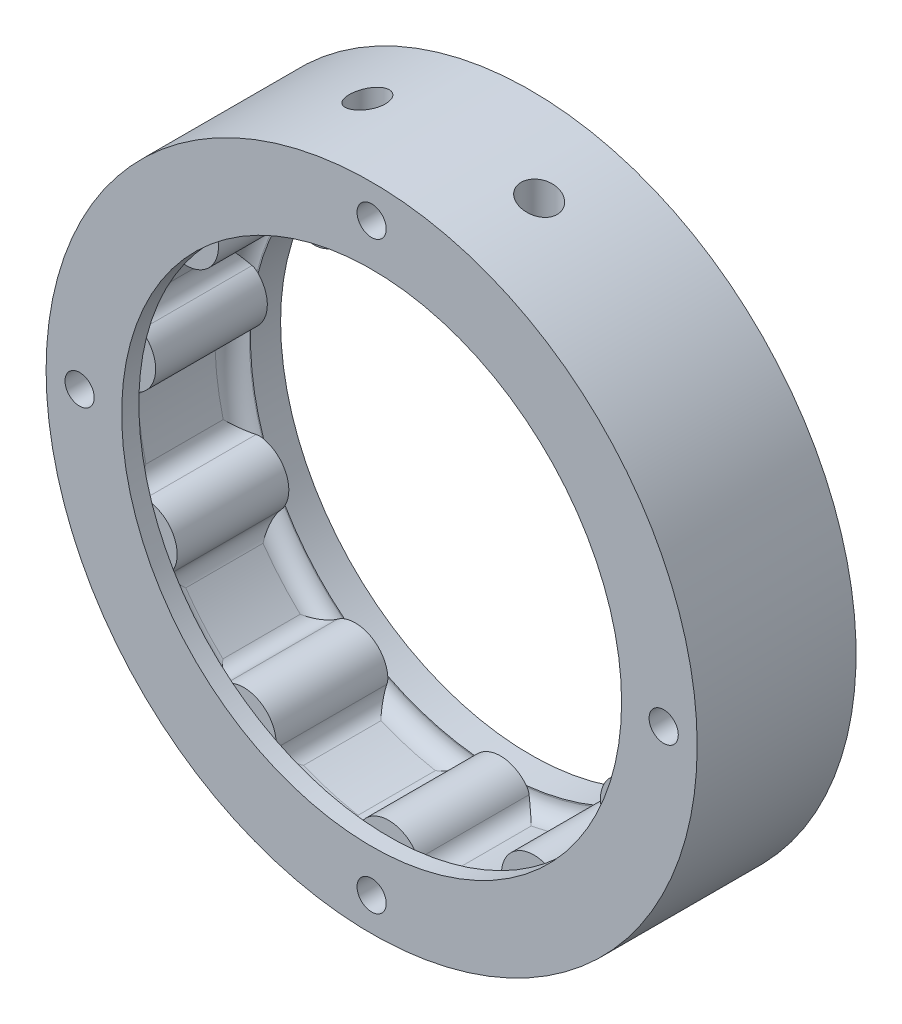
SolidWorks part; units mm, degrees
ref_plane "前视基准面" through (0, 0, 0) normal (0, 0, 1) x (1, 0, 0)
ref_plane "上视基准面" through (0, 0, 0) normal (0, 1, 0) x (1, 0, 0)
ref_plane "右视基准面" through (0, 0, 0) normal (1, 0, 0) x (0, 0, -1)
sketch "草图1" plane through (0, 0, 0) normal (0, 0, 1) x (1, 0, 0)
  arc A0 (-31.2338, 0.6797) -> (-29.7771, -9.4517) centre (0, 0) ccw
  arc A1 (3.7723, -31.0126) -> (-3.7723, -31.0126) centre (0, -31.2412) ccw
  arc A2 (-13.5933, -28.1289) -> (-19.9401, -24.05) centre (-16.8903, -26.2818) ccw
  arc A3 (-26.643, -16.3145) -> (-29.7771, -9.4517) centre (-28.418, -12.9781) ccw
  arc A4 (-31.2338, 0.6797) -> (-30.1601, 8.1474) centre (-30.9232, 4.4461) ccw
  arc A5 (-25.9081, 17.4581) -> (-20.9675, 23.1598) centre (-23.6105, 20.4586) ccw
  arc A6 (-12.3567, 28.6936) -> (-5.1178, 30.8191) centre (-8.8017, 29.9757) ccw
  arc A7 (5.1178, 30.8191) -> (12.3567, 28.6936) centre (8.8017, 29.9757) ccw
  arc A8 (20.9675, 23.1598) -> (25.9081, 17.4581) centre (23.6105, 20.4586) ccw
  arc A9 (30.1601, 8.1474) -> (31.2338, 0.6797) centre (30.9232, 4.4461) ccw
  arc A10 (29.7771, -9.4517) -> (26.643, -16.3145) centre (28.418, -12.9781) ccw
  arc A11 (19.9401, -24.05) -> (13.5933, -28.1289) centre (16.8903, -26.2818) ccw
  arc A13 (-25.9081, 17.4581) -> (-30.1601, 8.1474) centre (0, 0) ccw
  arc A14 (-12.3567, 28.6936) -> (-20.9675, 23.1598) centre (0, 0) ccw
  arc A15 (5.1178, 30.8191) -> (-5.1178, 30.8191) centre (0, 0) ccw
  arc A16 (20.9675, 23.1598) -> (12.3567, 28.6936) centre (0, 0) ccw
  arc A17 (30.1601, 8.1474) -> (25.9081, 17.4581) centre (0, 0) ccw
  arc A18 (29.7771, -9.4517) -> (31.2338, 0.6797) centre (0, 0) ccw
  arc A19 (-26.643, -16.3145) -> (-19.9401, -24.05) centre (0, 0) ccw
  arc A20 (-13.5933, -28.1289) -> (-3.7723, -31.0126) centre (0, 0) ccw
  arc A21 (3.7723, -31.0126) -> (13.5933, -28.1289) centre (0, 0) ccw
  arc A22 (19.9401, -24.05) -> (26.643, -16.3145) centre (0, 0) ccw
  circle A23 centre (0, -34) radius 1.7
  circle A24 centre (-34, 0) radius 1.7
  circle A25 centre (0, 34) radius 1.7
  circle A26 centre (34, 0) radius 1.7
  circle A29 centre (0, 0) radius 37.9
  point P28 (0, 0)
  point P52 (0, 0)
  dimension "D1" = 11
  dimension "D2" = 34
  dimension "D3" = 4
extrude "凸台-拉伸1" add sketch "草图1" along normal blind 13
sketch "草图2" plane through (0, 0, 0) normal (0, 0, -1) x (-1, 0, 0)
  circle A0 centre (0, 0) radius 29.1
  circle A1 centre (0, 0) radius 37.9
extrude "凸台-拉伸2" add sketch "草图2" along normal blind 3.5
sketch "草图3" plane through (0, 0, 13) normal (0, 0, 1) x (1, 0, 0)
  circle A0 centre (0, 0) radius 29.1
  circle A1 centre (0, 0) radius 37.9
extrude "凸台-拉伸3" add sketch "草图3" along normal blind 2
fillet "圆角1" radius 2 44 edges at (31.2338, 0.6797, 6.5) (30.9232, -4.4461, 13) (29.7771, -9.4517, 6.5) (30.9232, -4.4461, 0) (26.643, -16.3145, 6.5) (23.6105, -20.4586, 13) (19.9401, -24.05, 6.5) (23.6105, -20.4586, 0) (13.5933, -28.1289, 6.5) (8.8017, -29.9757, 13) (3.7723, -31.0126, 6.5) (8.8017, -29.9757, 0) (-3.7723, -31.0126, 6.5) (-8.8017, -29.9757, 13) (-13.5933, -28.1289, 6.5) (-8.8017, -29.9757, 0) (-19.9401, -24.05, 6.5) (-23.6105, -20.4586, 13) (-26.643, -16.3145, 6.5) (-23.6105, -20.4586, 0) (-29.7771, -9.4517, 6.5) (-30.9232, -4.4461, 13) (-31.2338, 0.6797, 6.5) (-30.9232, -4.4461, 0) (-30.1601, 8.1474, 6.5) (-28.418, 12.9781, 13) (-25.9081, 17.4581, 6.5) (-28.418, 12.9781, 0) (-20.9675, 23.1598, 6.5) (-16.8903, 26.2818, 13) (-12.3567, 28.6936, 6.5) (-16.8903, 26.2818, 0) (-5.1178, 30.8191, 6.5) (0, 31.2412, 13) (5.1178, 30.8191, 6.5) (0, 31.2412, 0) (12.3567, 28.6936, 6.5) (16.8903, 26.2818, 13) (20.9675, 23.1598, 6.5) (16.8903, 26.2818, 0) (25.9081, 17.4581, 6.5) (28.418, 12.9781, 13) (30.1601, 8.1474, 6.5) (28.418, 12.9781, 0)
sketch "草图4" plane through (0, 0, -3.5) normal (0, 0, -1) x (-1, 0, 0)
  circle A0 centre (0, -34) radius 1.7
  circle A1 centre (-34, 0) radius 1.7
  circle A2 centre (0, 34) radius 1.7
  circle A3 centre (34, 0) radius 1.7
  point P12 (0, 0)
  dimension "D1" = 4
extrude "切除-拉伸3" cut sketch "草图4" against normal blind 21
ref_plane "基准面1" through (0, 38, 0) normal (0, 1, 0) x (1, 0, 0)
ref_plane "基准面2" through (0, -38, 0) normal (0, 1, 0) x (1, 0, 0)
sketch "草图6" plane through (0, 38, 0) normal (0, 1, 0) x (1, 0, 0)
  line L0 (0, 3.5) -> (0, -5.5) construction
  line L1 (37.9, 3.5) -> (-37.9, 3.5) construction
  line L2 (0, -5.5) -> (-10, -5.5) construction
  line L3 (0, -5.5) -> (10, -5.5) construction
  circle A0 centre (-10, -5.5) radius 2.1
  circle A1 centre (10, -5.5) radius 2.1
extrude "切除-拉伸4" cut sketch "草图6" against normal blind 6.5
sketch "草图7" plane through (0, -38, 0) normal (0, 1, 0) x (1, 0, 0)
  line L0 (0, 3.5) -> (0, -5.5) construction
  line L1 (37.9, 3.5) -> (-37.9, 3.5) construction
  line L2 (0, -5.5) -> (-10, -5.5) construction
  line L3 (0, -5.5) -> (10, -5.5) construction
  circle A0 centre (-10, -5.5) radius 2.1
  circle A1 centre (10, -5.5) radius 2.1
extrude "切除-拉伸6" cut sketch "草图7" along normal blind 6.5
